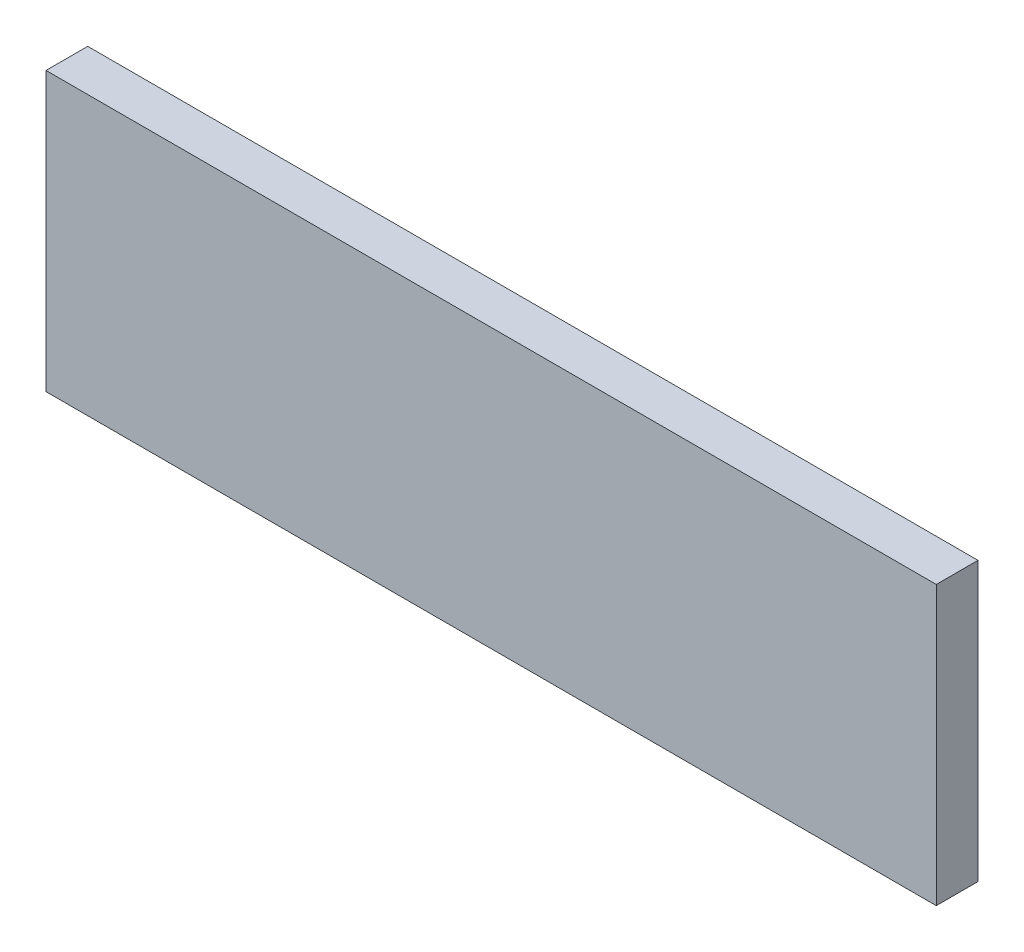
SolidWorks part; units mm, degrees
ref_plane "前视基准面" through (0, 0, 0) normal (0, 0, 1) x (1, 0, 0)
ref_plane "上视基准面" through (0, 0, 0) normal (0, 1, 0) x (1, 0, 0)
ref_plane "右视基准面" through (0, 0, 0) normal (1, 0, 0) x (0, 0, -1)
sketch "草图1" plane through (0, 0, 0) normal (0, 1, 0) x (1, 0, 0)
  line L1 (0, 0) -> (320, 0)
  line L2 (0, 0) -> (0, 15)
  line L3 (0, 15) -> (320, 15)
  line L4 (320, 0) -> (320, 15)
  dimension "D1" = 15
  dimension "D2" = 320
extrude "凸台-拉伸1" add sketch "草图1" along normal blind 100
